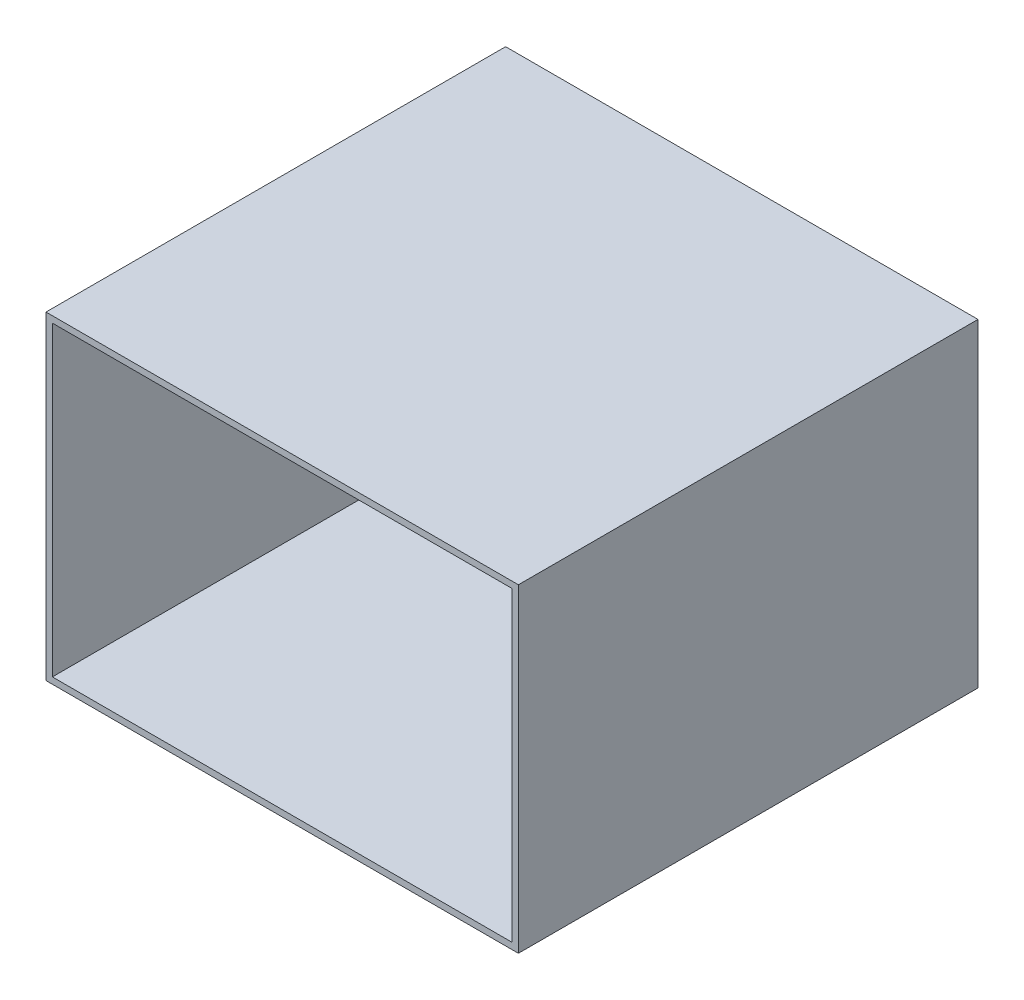
SolidWorks part; units mm, degrees
material "Acrylic (Medium-high impact)"
ref_plane "Front Plane" through (0, 0, 0) normal (0, 0, 1) x (1, 0, 0)
ref_plane "Top Plane" through (0, 0, 0) normal (0, 1, 0) x (1, 0, 0)
ref_plane "Right Plane" through (0, 0, 0) normal (1, 0, 0) x (0, 0, -1)
sketch "Sketch1" plane through (0, 0, 0) normal (0, 0, 1) x (1, 0, 0)
  line L0 (0, 152.4) -> (457.2, 152.4) construction
  line L1 (0, 0) -> (457.2, 0)
  line L2 (0, 0) -> (0, 304.8)
  line L3 (0, 304.8) -> (457.2, 304.8)
  line L4 (457.2, 0) -> (457.2, 304.8)
  line L5 (228.6, 304.8) -> (228.6, 0) construction
  circle A0 centre (228.6, 152.4) radius 25.4
  dimension "D3" = 50.8
  dimension "D1" = 457.2
  dimension "D2" = 304.8
extrude "Chamber Base" add sketch "Sketch1" along normal blind 6.35
sketch "Sketch2" plane through (457.2, 0, 0) normal (1, 0, 0) x (0, 0, -1)
  line L1 (0, 0) -> (-457.2, 0)
  line L2 (0, 0) -> (0, 304.8)
  line L3 (0, 304.8) -> (-457.2, 304.8)
  line L4 (-457.2, 0) -> (-457.2, 304.8)
  dimension "D1" = 304.8
  dimension "D2" = 457.2
extrude "Back wall" add sketch "Sketch2" along normal blind 6.35
sketch "Sketch3" plane through (0, 304.8, 0) normal (0, 1, 0) x (1, 0, 0)
  line L0 (463.55, 0) -> (463.55, -457.2) construction
  line L1 (0, 0) -> (463.55, 0)
  line L2 (0, 0) -> (0, -457.2)
  line L3 (0, -457.2) -> (463.55, -457.2)
  line L4 (463.55, 0) -> (463.55, -457.2)
  dimension "D1" = 457.2
extrude "Side wall 2" add sketch "Sketch3" along normal blind 6.35
sketch "Sketch5" plane through (0, 0, 0) normal (0, -1, 0) x (1, 0, 0)
  line L0 (463.55, 457.2) -> (463.55, 0) construction
  line L1 (0, 0) -> (463.55, 0)
  line L2 (0, 0) -> (0, 457.2)
  line L3 (0, 457.2) -> (463.55, 457.2)
  line L4 (463.55, 0) -> (463.55, 457.2)
  dimension "D1" = 457.2
extrude "Side wall 3" add sketch "Sketch5" along normal blind 6.35
sketch "Sketch6" plane through (0, 0, 0) normal (-1, 0, 0) x (0, 0, 1)
  line L1 (0, 311.15) -> (457.2, 311.15)
  line L2 (0, 311.15) -> (0, -6.35)
  line L3 (0, -6.35) -> (457.2, -6.35)
  line L4 (457.2, 311.15) -> (457.2, -6.35)
extrude "Boss-Extrude1" add sketch "Sketch6" along normal blind 6.35
